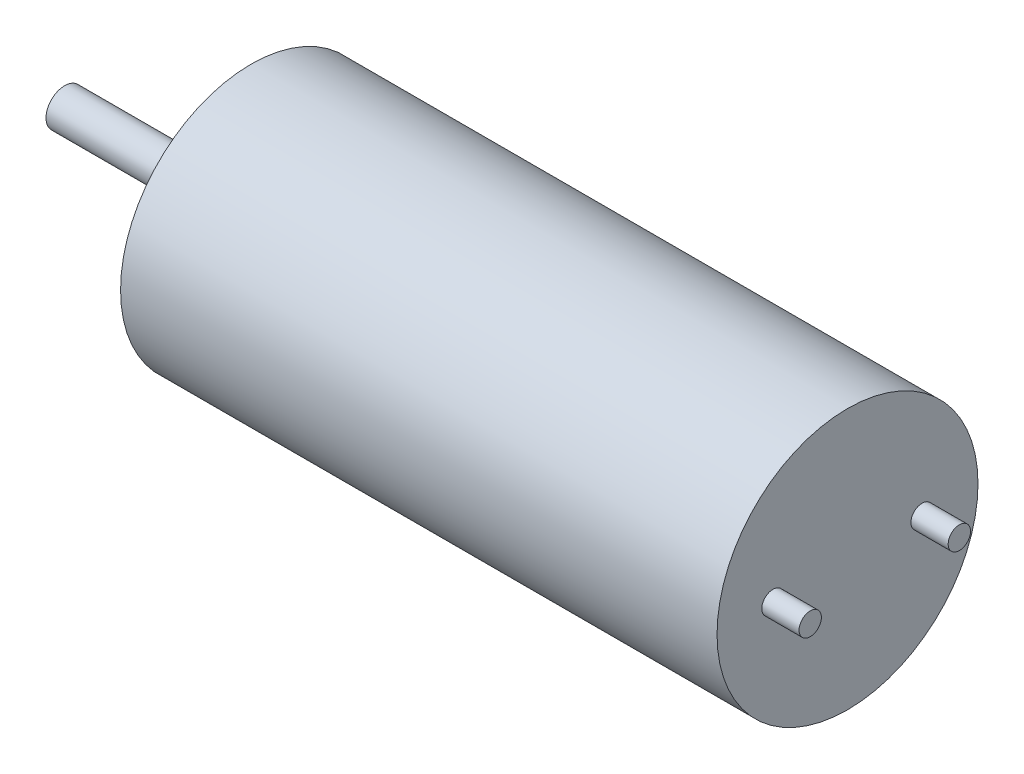
SolidWorks part; units mm, degrees
ref_plane "Front Plane" through (0, 0, 0) normal (0, 0, 1) x (1, 0, 0)
ref_plane "Top Plane" through (0, 0, 0) normal (0, 1, 0) x (1, 0, 0)
ref_plane "Right Plane" through (0, 0, 0) normal (1, 0, 0) x (0, 0, -1)
sketch "Sketch1" plane through (0, 0, 0) normal (1, 0, 0) x (0, 0, -1)
  circle A0 centre (0, 0) radius 3.5
  dimension "D1" = 7
extrude "Boss-Extrude1" add sketch "Sketch1" along normal blind 16
sketch "Sketch2" plane through (0, 0, 0) normal (-1, 0, 0) x (0, 0, 1)
  circle A0 centre (0, 0) radius 1.2
  dimension "D1" = 2.4
extrude "Boss-Extrude2" add sketch "Sketch2" along normal blind 0.8
sketch "Sketch3" plane through (-0.8, 0, 0) normal (-1, 0, 0) x (0, 0, 1)
  circle A0 centre (0, 0) radius 0.5
  dimension "D1" = 1
extrude "Boss-Extrude3" add sketch "Sketch3" along normal blind 4.2
sketch "Sketch4" plane through (16, 0, 0) normal (1, 0, 0) x (0, 0, -1)
  line L0 (-2, 0) -> (2, 0) construction
  circle A0 centre (-2, 0) radius 0.3
  circle A1 centre (2, 0) radius 0.3
  point P4 (0, 0)
  dimension "D2" = 0.6
  dimension "D1" = 4
extrude "Boss-Extrude4" add sketch "Sketch4" along normal blind 1
